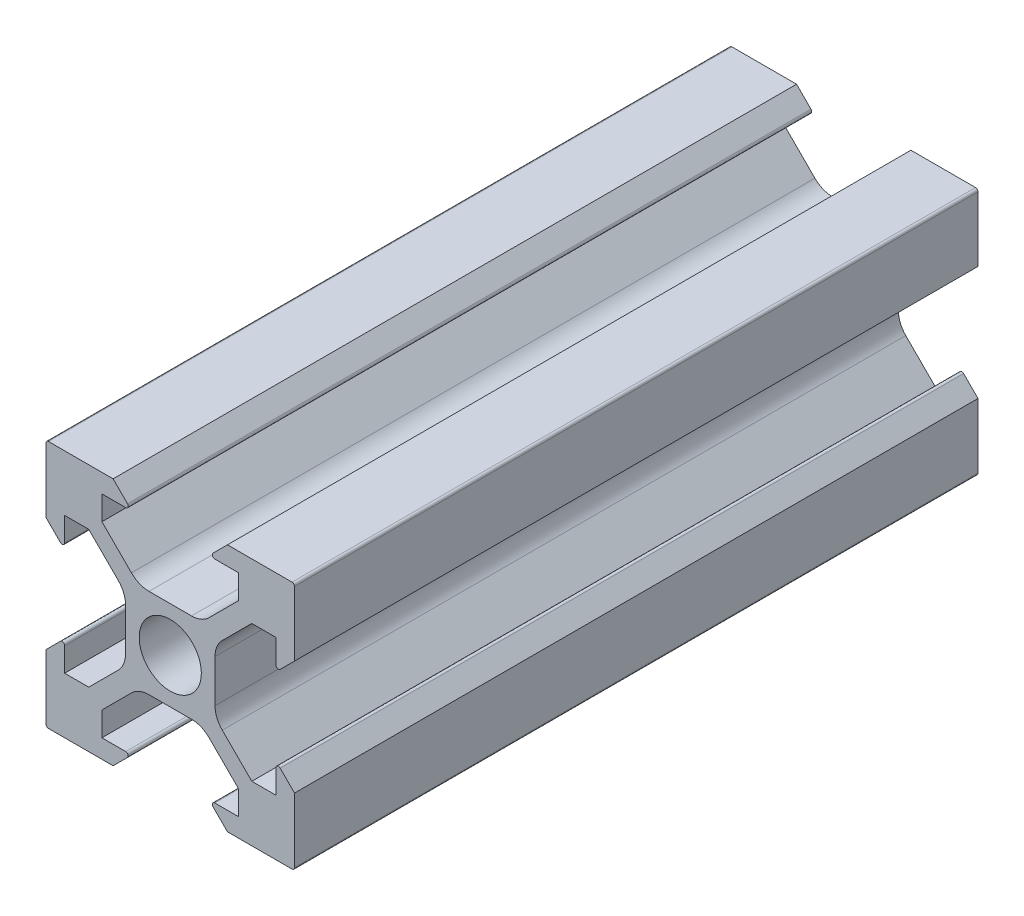
SolidWorks part; units mm, degrees
material "Liga 1350"
ref_plane "Plano frontal" through (0, 0, 0) normal (0, 0, 1) x (1, 0, 0)
ref_plane "Plano superior" through (0, 0, 0) normal (0, 1, 0) x (1, 0, 0)
ref_plane "Plano direito" through (0, 0, 0) normal (1, 0, 0) x (0, 0, -1)
sketch "Esboço1" plane through (0, 0, 0) normal (0, 0, 1) x (1, 0, 0)
  line L0 (0, 13.8681) -> (0, -15.879) construction
  line L1 (-4.6, -10) -> (-9.8, -10)
  line L2 (-3.4414, -8.8414) -> (-4.6, -10)
  line L3 (-4.1858, -3.1251) -> (-6.5607, -5.5)
  line L4 (-10, 9.8) -> (-10, 4.6)
  line L5 (-5.5, -8.5) -> (-3.5828, -8.5)
  line L6 (-5.5, -8.5) -> (-5.5, -6.5607)
  line L7 (-8.5, -5.5) -> (-8.5, -3.5828)
  line L8 (-21.5514, 0) -> (2.5, 0) construction
  line L9 (-3.1251, 4.1858) -> (-5.5, 6.5607)
  line L10 (-8.8414, -3.4414) -> (-10, -4.6)
  line L11 (-8.5, 5.5) -> (-6.5607, 5.5)
  line L12 (-8.8414, 3.4414) -> (-10, 4.6)
  line L13 (-8.5, -5.5) -> (-6.5607, -5.5)
  line L14 (-8.5, 5.5) -> (-8.5, 3.5828)
  line L15 (-3.1251, -4.1858) -> (-5.5, -6.5607)
  line L16 (-21.5514, 0) -> (20.6623, 0) construction
  line L17 (-8.5, 10) -> (-8.5, -10) construction
  line L18 (-10, -9.8) -> (-10, -4.6)
  line L19 (-21.5514, 5.5) -> (20.6623, 5.5) construction
  line L21 (-10, 10) -> (-10, -10) construction
  line L22 (3.6, 1.7109) -> (3.6, 0) construction
  line L23 (21.5514, 0) -> (-2.5, 0) construction
  line L24 (4.6, 10) -> (9.8, 10)
  line L25 (-5.5, 8.5) -> (-5.5, 6.5607)
  line L26 (3.4414, 8.8414) -> (4.6, 10)
  line L27 (-5.5, 8.5) -> (-3.5828, 8.5)
  line L28 (4.1858, 3.1251) -> (6.5607, 5.5)
  line L29 (5.5, 8.5) -> (3.5828, 8.5)
  line L30 (5.5, 8.5) -> (5.5, 6.5607)
  line L31 (-3.6, 1.7109) -> (-3.6, -1.7109)
  line L33 (10, -9.8) -> (10, -4.6)
  line L34 (-4.1858, 3.1251) -> (-6.5607, 5.5)
  line L35 (-3.4414, 8.8414) -> (-4.6, 10)
  line L36 (-4.6, 10) -> (-9.8, 10)
  line L37 (3.1251, -4.1858) -> (5.5, -6.5607)
  line L38 (8.5, 5.5) -> (8.5, 3.5828)
  line L39 (8.5, -5.5) -> (6.5607, -5.5)
  line L40 (8.8414, 3.4414) -> (10, 4.6)
  line L41 (8.5, 5.5) -> (6.5607, 5.5)
  line L42 (8.8414, -3.4414) -> (10, -4.6)
  line L43 (3.1251, 4.1858) -> (5.5, 6.5607)
  line L44 (8.5, -5.5) -> (8.5, -3.5828)
  line L45 (5.5, -8.5) -> (5.5, -6.5607)
  line L46 (5.5, -8.5) -> (3.5828, -8.5)
  line L47 (10, 9.8) -> (10, 4.6)
  line L48 (4.1858, -3.1251) -> (6.5607, -5.5)
  line L49 (3.4414, -8.8414) -> (4.6, -10)
  line L50 (4.6, -10) -> (9.8, -10)
  line L51 (-1.7109, 3.6) -> (1.7109, 3.6)
  line L52 (3.6, 1.7109) -> (3.6, -1.7109)
  line L53 (1.7109, -3.6) -> (-1.7109, -3.6)
  circle A0 centre (0, 0) radius 2.5
  arc A1 (-3.6, 1.7109) -> (-4.1858, 3.1251) centre (-5.6, 1.7109) ccw
  arc A2 (-8.5, 3.5828) -> (-8.8414, 3.4414) centre (-8.7, 3.5828) cw
  arc A3 (-9.8, 10) -> (-10, 9.8) centre (-9.8, 9.8) ccw
  arc A4 (-1.7109, 3.6) -> (-3.1251, 4.1858) centre (-1.7109, 5.6) cw
  arc A5 (-3.5828, 8.5) -> (-3.4414, 8.8414) centre (-3.5828, 8.7) ccw
  arc A6 (-3.5828, -8.5) -> (-3.4414, -8.8414) centre (-3.5828, -8.7) cw
  arc A7 (-1.7109, -3.6) -> (-3.1251, -4.1858) centre (-1.7109, -5.6) ccw
  arc A8 (-9.8, -10) -> (-10, -9.8) centre (-9.8, -9.8) cw
  arc A9 (-8.5, -3.5828) -> (-8.8414, -3.4414) centre (-8.7, -3.5828) ccw
  arc A10 (-3.6, -1.7109) -> (-4.1858, -3.1251) centre (-5.6, -1.7109) cw
  arc A11 (3.6, -1.7109) -> (4.1858, -3.1251) centre (5.6, -1.7109) ccw
  arc A12 (8.5, -3.5828) -> (8.8414, -3.4414) centre (8.7, -3.5828) cw
  arc A13 (9.8, -10) -> (10, -9.8) centre (9.8, -9.8) ccw
  arc A14 (1.7109, -3.6) -> (3.1251, -4.1858) centre (1.7109, -5.6) cw
  arc A15 (3.5828, -8.5) -> (3.4414, -8.8414) centre (3.5828, -8.7) ccw
  arc A16 (3.5828, 8.5) -> (3.4414, 8.8414) centre (3.5828, 8.7) cw
  arc A17 (1.7109, 3.6) -> (3.1251, 4.1858) centre (1.7109, 5.6) ccw
  arc A18 (9.8, 10) -> (10, 9.8) centre (9.8, 9.8) cw
  arc A19 (8.5, 3.5828) -> (8.8414, 3.4414) centre (8.7, 3.5828) ccw
  arc A20 (3.6, 1.7109) -> (4.1858, 3.1251) centre (5.6, 1.7109) cw
  point P0 (0, 0)
  point P45 (-3.6, 2.5393)
extrude "Ressalto-extrusão1" add sketch "Esboço1" along normal blind 55
